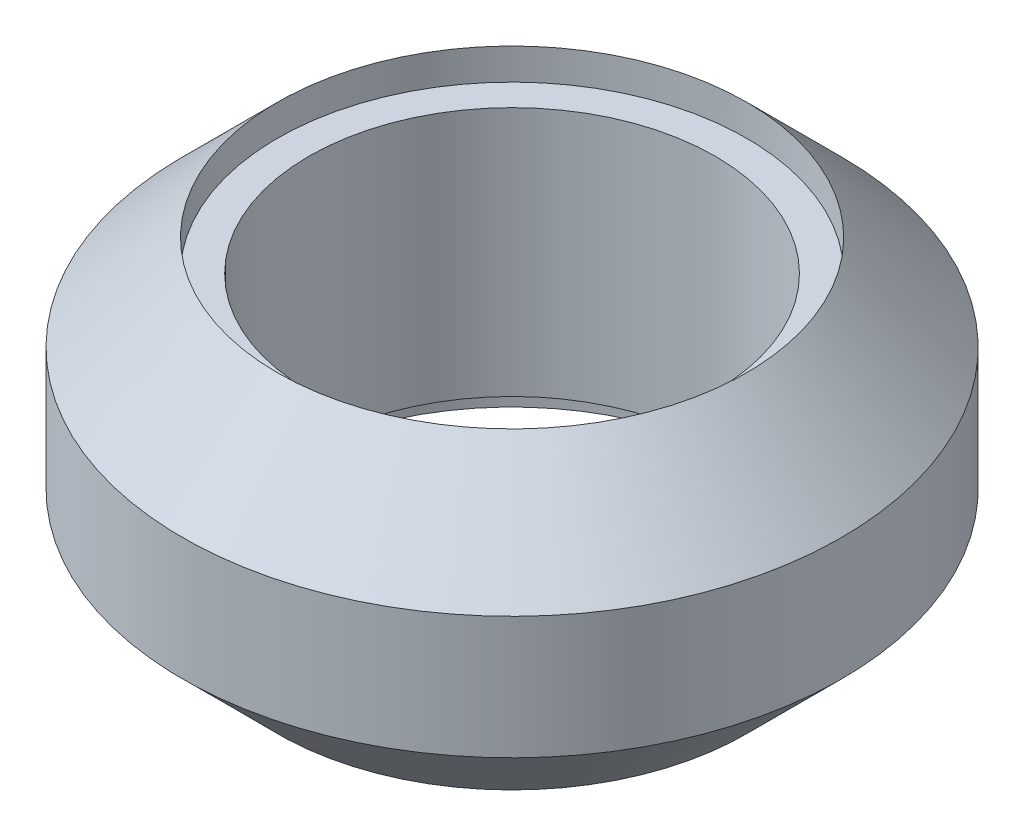
SolidWorks part; units mm, degrees
ref_plane "Front Plane" through (0, 0, 0) normal (0, 0, 1) x (1, 0, 0)
ref_plane "Top Plane" through (0, 0, 0) normal (0, 1, 0) x (1, 0, 0)
ref_plane "Right Plane" through (0, 0, 0) normal (1, 0, 0) x (0, 0, -1)
sketch "Sketch1" plane through (0, 0, 0) normal (0, 1, 0) x (1, 0, 0)
  circle A2 centre (0, 0) radius 7.5
  dimension "D1" = 15
extrude "Boss-Extrude3" add sketch "Sketch1" along normal blind 10
sketch "Sketch51" plane through (0, 0, 0) normal (0, 0, 1) x (1, 0, 0)
  line L0 (-7.5, 10) -> (-10.5406, 6.9594)
  line L3 (7.5, 10) -> (10.5406, 6.9594)
  line L4 (7.5, 0) -> (10.5406, 3.0406)
  line L6 (-7.5, 0) -> (-10.5406, 3.0406)
  dimension "D1" = 4.3
ref_plane "Plane4" through (0, 6.9594, 0) normal (0, 1, 0) x (1, 0, 0)
ref_plane "Plane5" through (0, 3.0406, 0) normal (0, -1, 0) x (1, 0, 0)
sketch "Sketch54" plane through (0, 6.9594, 0) normal (0, 1, 0) x (1, 0, 0)
  circle A1 centre (0, 0) radius 10.5406
extrude "Boss-Extrude5" add sketch "Sketch54" along normal up to vertex (3.0406 mm away) draft 45 contours A1 up to point (7.5, 10, 0)
sketch "Sketch55" plane through (0, 3.0406, 0) normal (0, -1, 0) x (1, 0, 0)
  circle A0 centre (0, 0) radius 10.5406
extrude "Boss-Extrude6" add sketch "Sketch55" along normal up to vertex (3.0406 mm away) draft 45 contours A0 up to point (-7.5, 0, 0)
sketch "Sketch56" plane through (0, 6.9594, 0) normal (0, -1, 0) x (-1, 0, 0)
  circle A0 centre (0, 0) radius 10.5406
  circle A1 centre (0, 0) radius 10.5406 construction
extrude "Boss-Extrude7" add sketch "Sketch56" along normal up to surface (3.9189 mm away) up to face at (0, 3.0406, -7.5)
sketch "Sketch53" plane through (0, 10, 0) normal (0, 1, 0) x (1, 0, 0)
  circle A0 centre (0, 0) radius 6.5
  dimension "D1" = 13
extrude "Cut-Extrude7" cut sketch "Sketch53" against normal through all
sketch "Sketch57" plane through (0, 0, 0) normal (0, -1, 0) x (-1, 0, 0)
  circle A0 centre (0, 0) radius 6.5
  circle A2 centre (0, 0) radius 7.5 construction
  circle A4 centre (0, 0) radius 6.5 construction
  circle A8 centre (0, 0) radius 7.5
extrude "Cut-Extrude8" cut sketch "Sketch57" against normal blind 1
sketch "Sketch59" plane through (0, 10, 0) normal (0, 1, 0) x (1, 0, 0)
  circle A0 centre (0, 0) radius 6.5
  circle A3 centre (0, 0) radius 6.5 construction
  circle A4 centre (0, 0) radius 7.5
  circle A9 centre (0, 0) radius 7.5 construction
extrude "Cut-Extrude9" cut sketch "Sketch59" against normal blind 1
